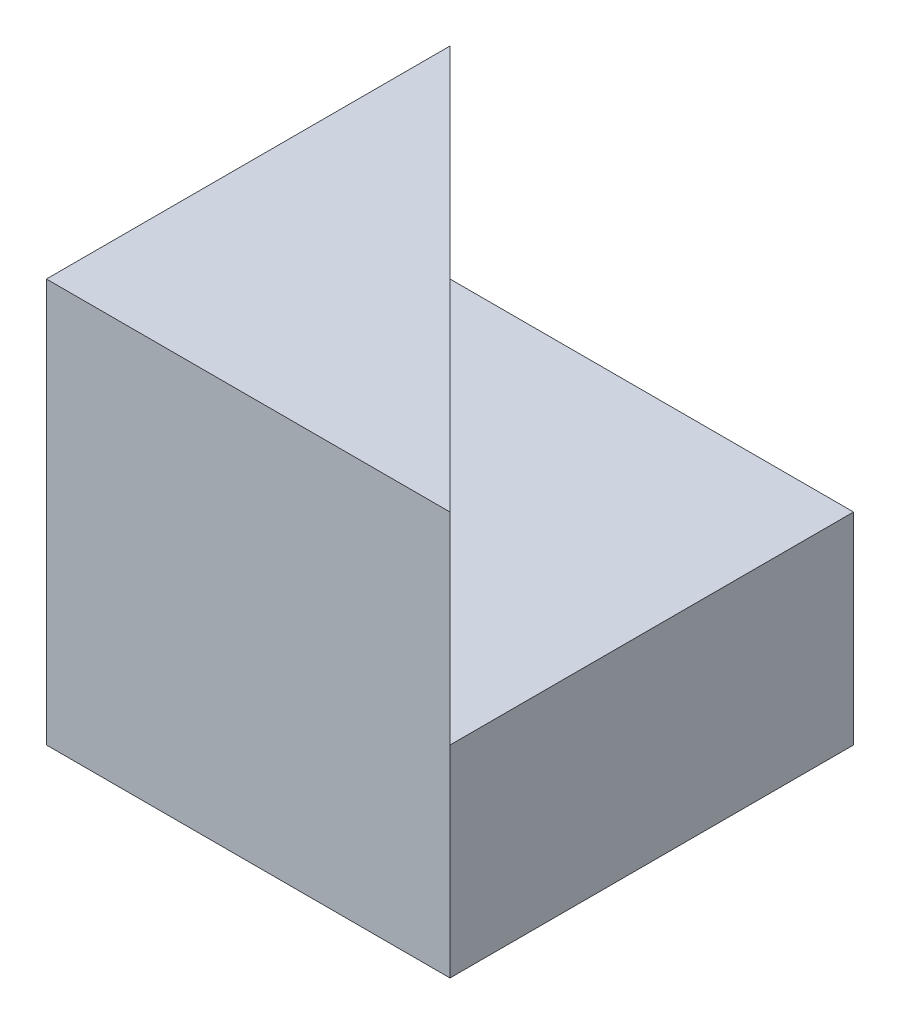
SolidWorks part; units mm, degrees
ref_plane "Front Plane" through (0, 0, 0) normal (0, 0, 1) x (1, 0, 0)
ref_plane "Top Plane" through (0, 0, 0) normal (0, 1, 0) x (1, 0, 0)
ref_plane "Right Plane" through (0, 0, 0) normal (1, 0, 0) x (0, 0, -1)
sketch "Sketch1" plane through (0, 0, 0) normal (0, 0, 1) x (1, 0, 0)
  line L1 (0, 0) -> (40, 0)
  line L2 (0, 0) -> (0, 40)
  line L3 (0, 40) -> (40, 40)
  line L4 (40, 0) -> (40, 40)
  dimension "D1" = 40
  dimension "D2" = 40
extrude "Boss-Extrude1" add sketch "Sketch1" along normal blind 40
sketch "Sketch2" plane through (0, 40, 0) normal (0, 1, 0) x (1, 0, 0)
  line L0 (0, 0) -> (40, -40)
  line L1 (40, -40) -> (40, 0)
  line L2 (40, 0) -> (0, 0)
extrude "Cut-Extrude1" cut sketch "Sketch2" against normal blind 20
